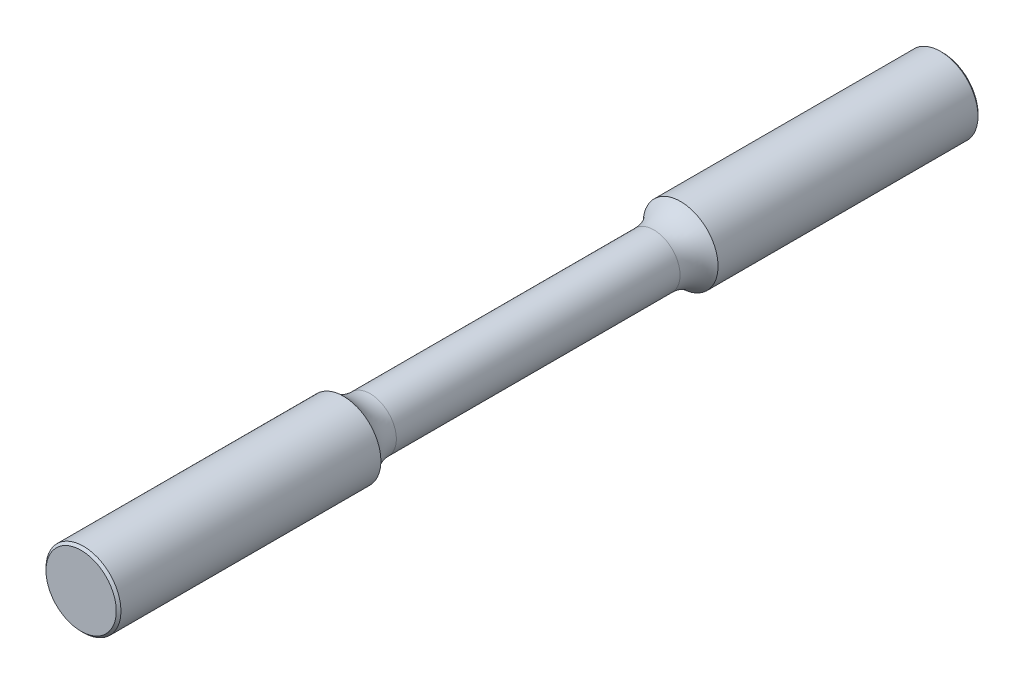
SolidWorks part; units mm, degrees
ref_plane "Front Plane" through (0, 0, 0) normal (0, 0, 1) x (1, 0, 0)
ref_plane "Top Plane" through (0, 0, 0) normal (0, 1, 0) x (1, 0, 0)
ref_plane "Right Plane" through (0, 0, 0) normal (1, 0, 0) x (0, 0, -1)
sketch "Sketch1" plane through (0, 0, 0) normal (0, 1, 0) x (1, 0, 0)
  line L0 (0, 73.025) -> (0, -73.025)
  line L1 (0, -73.025) -> (6.35, -73.025)
  line L2 (6.35, -73.025) -> (6.35, -28.575)
  line L3 (4.445, -24.0402) -> (4.445, 24.0402)
  line L4 (0, 73.025) -> (6.35, 73.025)
  line L5 (6.35, 73.025) -> (6.35, 28.575)
  arc A0 (4.445, -24.0402) -> (6.35, -28.575) centre (10.795, -24.0402) ccw
  arc A1 (4.445, 24.0402) -> (6.35, 28.575) centre (10.795, 24.0402) cw
  point P4 (0, 0)
  dimension "D7" = 6.35
  dimension "D8" = 6.35
  dimension "D1" = 44.45
  dimension "D2" = 44.45
  dimension "D3" = 146.05
  dimension "D4" = 6.35
  dimension "D5" = 4.445
  dimension "D6" = 6.35
revolve "Revolve1" add sketch "Sketch1" angle 360 about L0
chamfer "Chamfer1" distance 0.3969 angle 45 2 edges at (-6.35, 0, -73.025) (-6.35, 0, 73.025)
